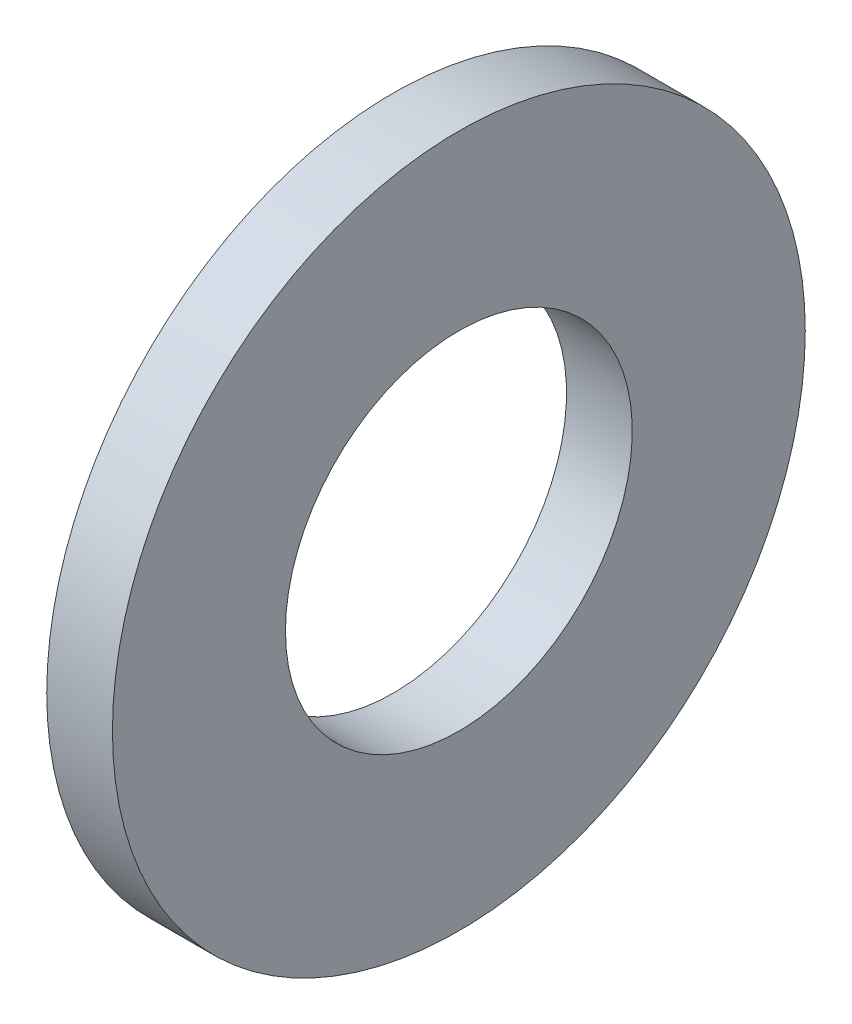
SolidWorks part; units mm, degrees
ref_plane "Plane1" through (0, 0, 0) normal (0, 0, 1) x (1, 0, 0)
ref_plane "Plane2" through (0, 0, 0) normal (0, 1, 0) x (1, 0, 0)
ref_plane "Plane3" through (0, 0, 0) normal (1, 0, 0) x (0, 0, -1)
sketch "Sketch1" plane through (0, 0, 0) normal (0, 0, 1) x (1, 0, 0)
  line L0 (-34.925, 0) -> (9.525, 0) construction
  line L1 (0, 5.5626) -> (0, 11.1125)
  line L2 (0, 11.1125) -> (-2.1082, 11.1125)
  line L3 (-2.1082, 11.1125) -> (-2.1082, 5.5626)
  line L4 (-2.1082, 5.5626) -> (0, 5.5626)
  dimension "Thickness" = 2.1082
  dimension "Inside_dia" = 11.1252
  dimension "Outside_dia" = 22.225
revolve "Base-Revolve" add sketch "Sketch1" angle 360 about L0
